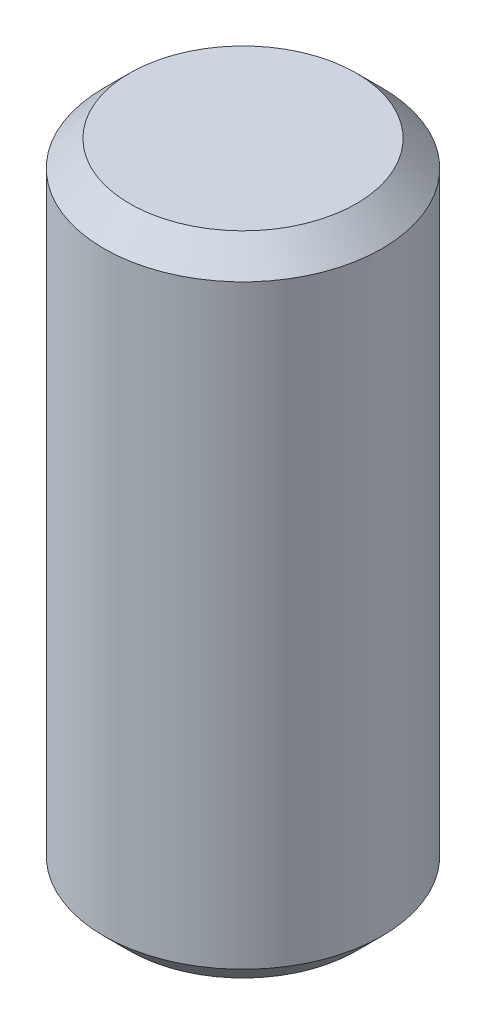
SolidWorks part; units mm, degrees
ref_plane "Front" through (0, 0, 0) normal (0, 0, 1) x (1, 0, 0)
ref_plane "Top" through (0, 0, 0) normal (0, 1, 0) x (1, 0, 0)
ref_plane "Right" through (0, 0, 0) normal (1, 0, 0) x (0, 0, -1)
sketch "Sketch1" plane through (0, 0, 0) normal (0, 0, 1) x (1, 0, 0)
  line L0 (0, 6.0802) -> (0, -6.0802) construction
  line L1 (0, -6.35) -> (2.7305, -6.35)
  line L2 (2.7305, -6.35) -> (2.7305, 6.35)
  line L3 (2.7305, 6.35) -> (0, 6.35)
  line L4 (0, 6.35) -> (0, -6.35)
  point P6 (0, 0)
  dimension "D1" = 5.461
  dimension "D2" = 12.7
revolve "Revolve1" add sketch "Sketch1" angle 360 about L0
chamfer "Chamfer1" distance 0.508 angle 45 2 edges at (0, -6.35, 2.7305) (0, 6.35, 2.7305)
